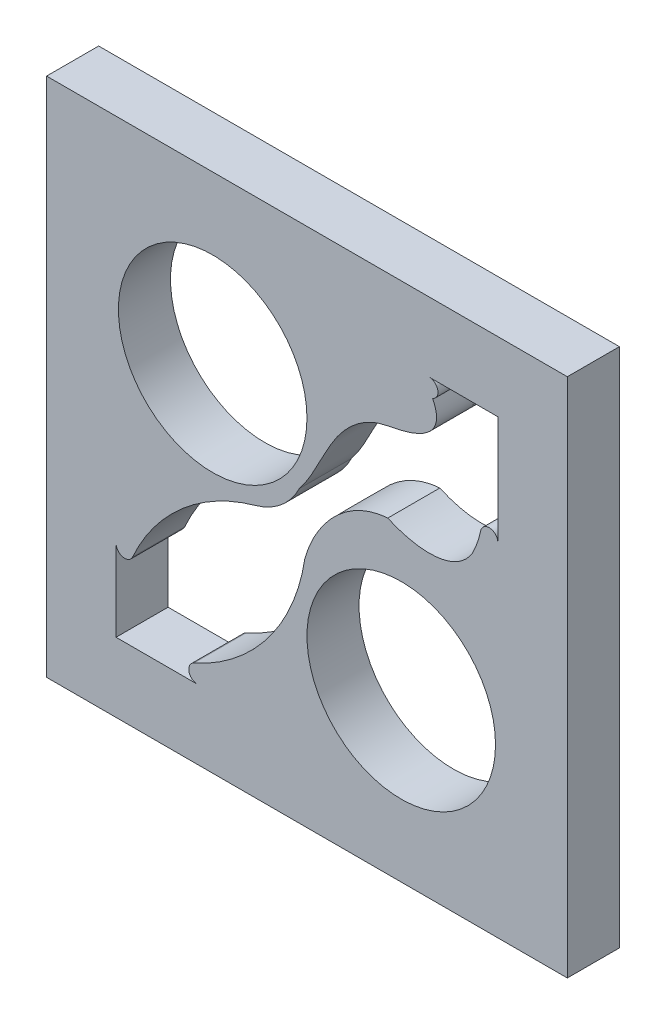
SolidWorks part; units mm, degrees
ref_plane "Alzado" through (0, 0, 0) normal (0, 0, 1) x (1, 0, 0)
ref_plane "Planta" through (0, 0, 0) normal (0, 1, 0) x (1, 0, 0)
ref_plane "Vista lateral" through (0, 0, 0) normal (1, 0, 0) x (0, 0, -1)
sketch "Croquis1" plane through (0, 0, 0) normal (0, 0, 1) x (1, 0, 0)
  line L1 (-15, 15) -> (15, 15)
  line L2 (-15, 15) -> (-15, -15)
  line L3 (-15, -15) -> (15, -15)
  line L4 (15, 15) -> (15, -15)
  line L6 (-15, -15) -> (-11, -11) construction
  line L11 (-11, -6.3096) -> (-11, -11)
  line L13 (-11, -11) -> (-6.3096, -11)
  line L14 (11, 11) -> (7.048, 11)
  line L15 (11, 4.7159) -> (11, 11)
  arc A0 (-10.0435, -6.5135) -> (-2.962, -0.4063) centre (0, -11) cw
  circle A2 centre (-5.4314, 5.4314) radius 5.4314
  arc A3 (-0.446, 1.6882) -> (-2.962, -0.4063) centre (-4.0391, 3.4459) cw
  arc A4 (-6.5135, -10.0435) -> (-0.124, -1.6471) centre (-11, 0) ccw
  circle A6 centre (5.4314, -5.4314) radius 5.4314
  arc A8 (-11, -6.3096) -> (-10.0435, -6.5135) centre (-10.5, -6.3096) ccw
  arc A9 (-6.3096, -11) -> (-6.5135, -10.0435) centre (-6.3096, -10.5) cw
  arc A10 (9.5247, 3.4459) -> (10.0107, 4.8186) centre (4.6533, 5.943) ccw
  arc A12 (11, 4.7159) -> (10.0107, 4.8186) centre (10.5, 4.7159) ccw
  arc A13 (7.048, 11) -> (7.239, 10.0379) centre (7.048, 10.5) cw
  spline S0 degree 3 poles (4.6533, 2.7734) (6.1381, 2.0966) (8.4671, 1.7565) (9.5247, 3.4459) knots 0 0 0 0 1 1 1 1
  spline S1 degree 3 poles (-0.446, 1.6882) (0.6002, 2.9978) (1.2595, 5.4126) (3.7235, 7.2688) (6.075, 7.5545) (8.017, 8.4997) (7.239, 10.0379) knots 0 0 0 0 0.408369 0.584002 0.707827 1 1 1 1
  spline S2 degree 3 poles (-0.3092, -2.5897) (-0.0128, -0.0523) (1.9546, 2.5912) (4.6533, 2.7734) knots 0 0 0 0 1 1 1 1
  point P0 (0, 0)
  point P6 (0, 0)
  dimension "D5" = 4
  dimension "D7" = 0.5
  dimension "D8" = 0.5
  dimension "D9" = 0.5
  dimension "D10" = 0.5
  dimension "D1" = 30
  dimension "D2" = 30
extrude "Saliente-Extruir1" add sketch "Croquis1" along normal blind 3
